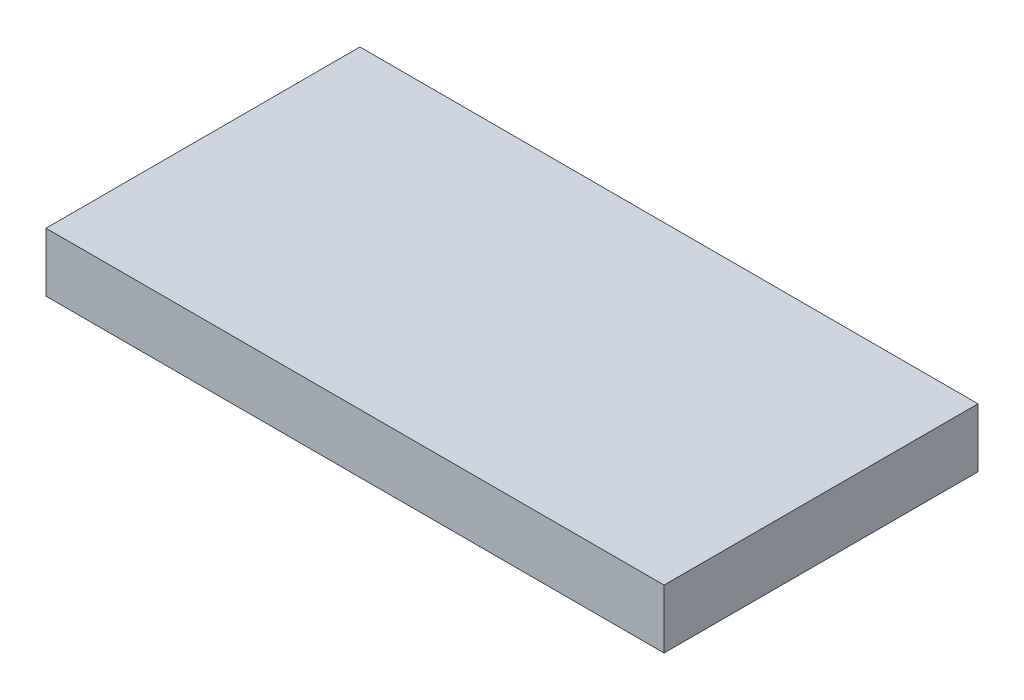
SolidWorks part; units mm, degrees
ref_plane "Front Plane" through (0, 0, 0) normal (0, 0, 1) x (1, 0, 0)
ref_plane "Top Plane" through (0, 0, 0) normal (0, 1, 0) x (1, 0, 0)
ref_plane "Right Plane" through (0, 0, 0) normal (1, 0, 0) x (0, 0, -1)
sketch "Sketch1" plane through (0, 0, 0) normal (0, 1, 0) x (1, 0, 0)
  line L0 (-2.55, 1.6) -> (-2.55, -1.6)
  line L1 (3.15, -1.6) -> (-3.15, -1.6)
  line L2 (3.15, -1.6) -> (3.15, 1.6)
  line L3 (3.15, 1.6) -> (-3.15, 1.6)
  line L4 (-3.15, -1.6) -> (-3.15, 1.6)
  line L5 (3.15, -1.6) -> (-3.15, 1.6) construction
  line L6 (3.15, 1.6) -> (-3.15, -1.6) construction
  line L7 (2.55, 1.6) -> (2.55, -1.6)
  point P0 (0, 0)
  dimension "D1" = 6.3
  dimension "D2" = 3.2
  dimension "D3" = 0.6
  dimension "D4" = 0.6
extrude "Boss-Extrude1" add sketch "Sketch1" along normal mid plane 0.6 contours L7 L3 L0 L1 | L4 L1 L0 L3 | L3 L7 L1 L2
